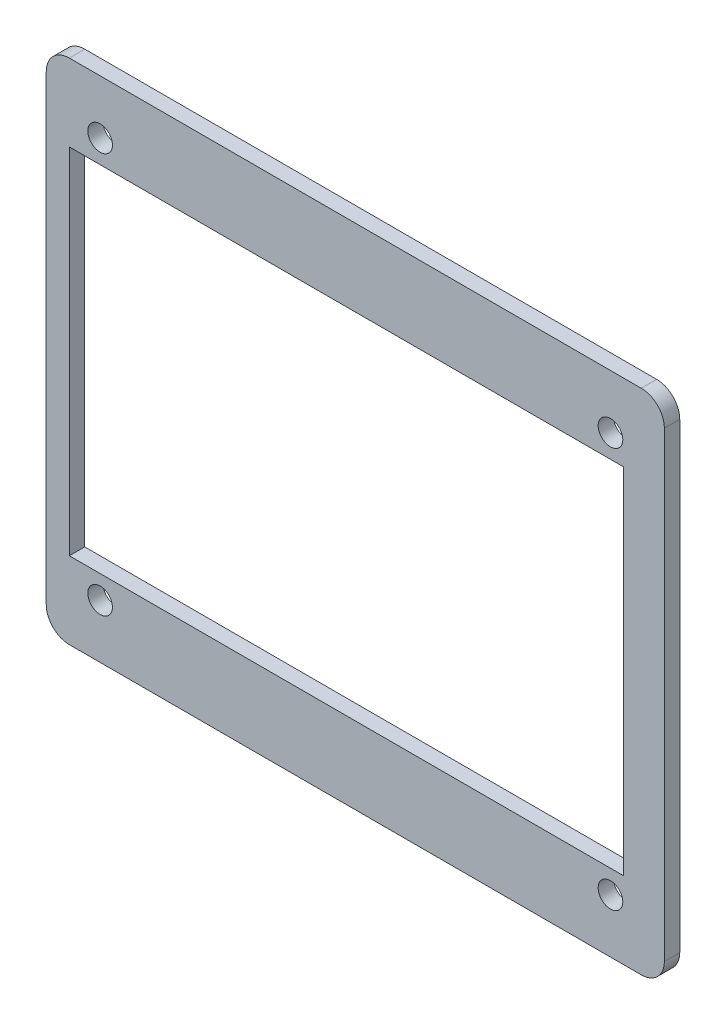
SolidWorks part; units mm, degrees
material "Acrylic (Medium-high impact)"
ref_plane "Front Plane" through (0, 0, 0) normal (0, 0, 1) x (1, 0, 0)
ref_plane "Top Plane" through (0, 0, 0) normal (0, 1, 0) x (1, 0, 0)
ref_plane "Right Plane" through (0, 0, 0) normal (1, 0, 0) x (0, 0, -1)
sketch "Sketch1" plane through (0, 0, 0) normal (0, 0, 1) x (1, 0, 0)
  line L1 (0, 0) -> (80.3, 0)
  line L2 (0, 0) -> (0, 66)
  line L3 (0, 66) -> (80.3, 66)
  line L4 (80.3, 0) -> (80.3, 66)
  dimension "D1" = 80.3
  dimension "D2" = 66
extrude "Boss-Extrude1" add sketch "Sketch1" along normal blind 2
hole_wizard "Ø3.2 (3.2) Diameter Hole1" positions "Sketch3" profile "Sketch2" hole size "Ø3.2" standard "ANSI Metric" end condition through all
sketch "Sketch3" plane through (0, 0, 2) normal (0, 0, 1) x (1, 0, 0)
  line L0 (0, 33) -> (80.3, 33) construction
  line L1 (0, 66) -> (0, 0) construction
  line L2 (80.3, 0) -> (80.3, 66) construction
  line L4 (7, 7) -> (7, 59) construction
  line L6 (7, 59) -> (73.3, 59) construction
  line L7 (73.3, 59) -> (73.3, 7) construction
  line L8 (73.3, 7) -> (7, 7) construction
  line L10 (40.15, 66) -> (40.15, 0) construction
  line L11 (80.3, 66) -> (0, 66) construction
  line L12 (0, 0) -> (80.3, 0) construction
  point P0 (7, 59)
  point P2 (73.3, 59)
  point P4 (73.3, 7)
  point P6 (7, 7)
  dimension "D1" = 66.3
  dimension "D2" = 52
  dimension "D3" = 26
  dimension "D4" = 33.15
sketch "Sketch2" plane through (7, 59, 2) normal (1, 0, 0) x (0, -1, 0)
  line L0 (0, 0) -> (0, 2)
  line L1 (0, 2) -> (1.6, 2)
  line L2 (1.6, 2) -> (1.6, 0)
  line L5 (1.6, 0) -> (0, 0)
  line L11 (0, -6.35) -> (0, 107.95) construction
  dimension "Thru Hole Dia." = 3.2
  dimension "Thru Hole Depth" = 2
fillet "Fillet1" radius 3 4 edges at (80.3, 66, 1) (80.3, 0, 1) (0, 0, 1) (0, 66, 1)
sketch "Sketch4" plane through (0, 0, 2) normal (0, 0, 1) x (1, 0, 0)
  line L0 (7, 59) -> (7, 7) construction
  line L1 (3, 10) -> (75, 10)
  line L2 (3, 10) -> (3, 56)
  line L3 (3, 56) -> (75, 56)
  line L4 (75, 10) -> (75, 56)
  line L5 (3, 33) -> (75, 33) construction
  line L6 (7, 59) -> (73.3, 59) construction
  line L7 (73.3, 59) -> (73.3, 7) construction
  line L8 (73.3, 7) -> (7, 7) construction
  line L9 (7, 33) -> (73.3, 33) construction
  dimension "D1" = 72
  dimension "D2" = 46
  dimension "D3" = 4
extrude "Cut-Extrude1" cut sketch "Sketch4" against normal through all
